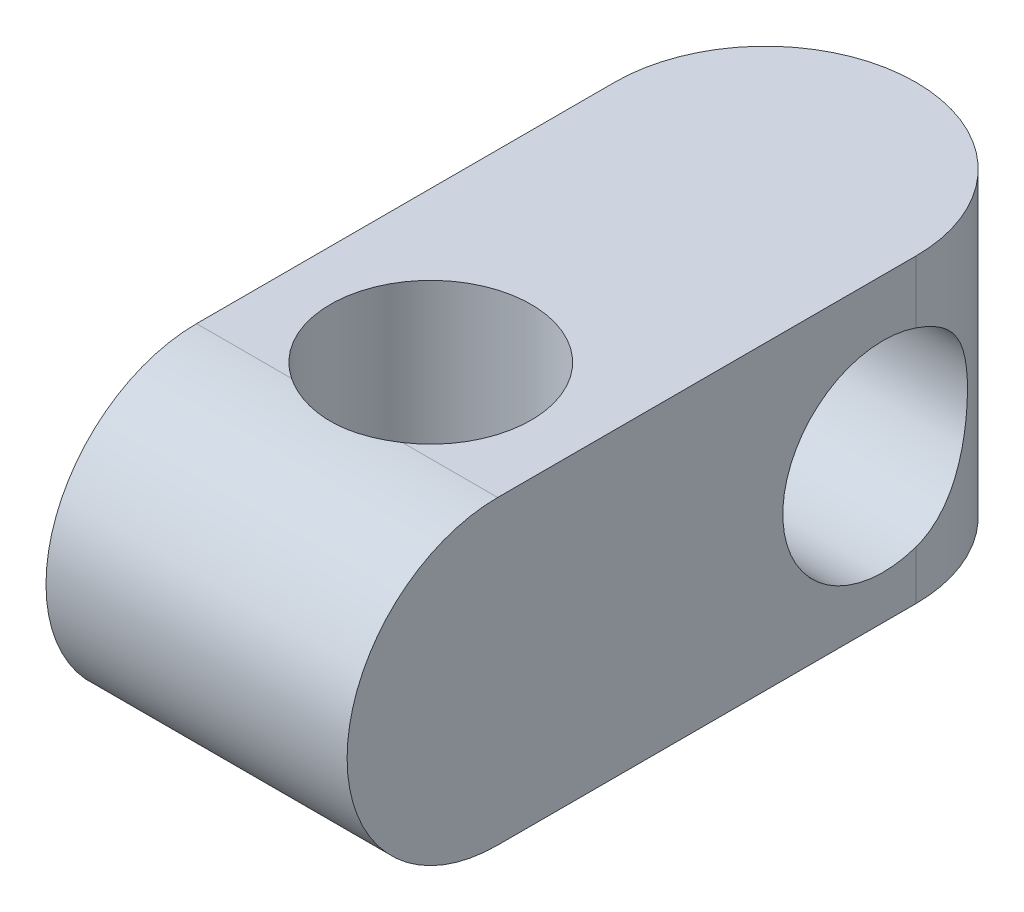
SolidWorks part; units mm, degrees
ref_plane "Front Plane" through (0, 0, 0) normal (0, 0, 1) x (1, 0, 0)
ref_plane "Top Plane" through (0, 0, 0) normal (0, 1, 0) x (1, 0, 0)
ref_plane "Right Plane" through (0, 0, 0) normal (1, 0, 0) x (0, 0, -1)
sketch "Sketch1" plane through (0, 0, 0) normal (0, 1, 0) x (1, 0, 0)
  line L1 (-9, -17) -> (9, -17)
  line L2 (-9, -17) -> (-9, 17)
  line L4 (9, -17) -> (9, 17)
  line L5 (-9, -17) -> (9, 17) construction
  line L6 (-9, 17) -> (9, -17) construction
  arc A0 (-9, 17) -> (9, 17) centre (0, 17) cw
  circle A1 centre (0, -3) radius 6
  point P0 (0, 0)
  dimension "D1" = 12
  dimension "D2" = 9
  dimension "D5" = 14
  dimension "D3" = 34
  dimension "D4" = 18
extrude "Boss-Extrude1" add sketch "Sketch1" along normal blind 18
sketch "Sketch2" plane through (9, 0, 0) normal (1, 0, 0) x (0, 0, -1)
  line L2 (-17, 18) -> (-17, 0) construction
  line L3 (-17, 0) -> (17, 0) construction
  line L4 (-17, 18) -> (17, 18) construction
  line L5 (-8, 18) -> (-17, 18)
  line L6 (-17, 18) -> (-17, 0)
  line L7 (-17, 0) -> (-8, 0)
  circle A0 centre (15.0457, 8.606) radius 6
  arc A1 (-8, 0) -> (-8, 18) centre (-8, 9) cw
  line M1 (-17, 0) -> (17, 0)
  line M2 (17, 0) -> (17, 18)
  line M3 (17, 18) -> (-17, 18)
  line M4 (-17, 18) -> (-17, 0)
  dimension "D1" = 12
extrude "Cut-Extrude3" cut sketch "Sketch2" against normal blind 18 contours A1 L6 M1 | A1 M4 M3 | A0 M2 | A0 M2
